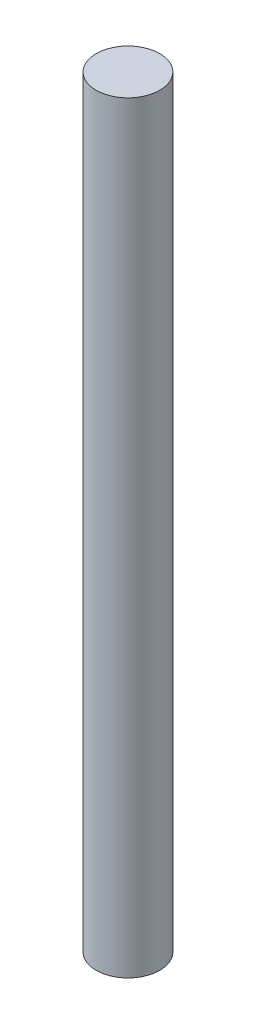
SolidWorks part; units mm, degrees
ref_plane "Front Plane" through (0, 0, 0) normal (0, 0, 1) x (1, 0, 0)
ref_plane "Top Plane" through (0, 0, 0) normal (0, 1, 0) x (1, 0, 0)
ref_plane "Right Plane" through (0, 0, 0) normal (1, 0, 0) x (0, 0, -1)
sketch "Sketch1" plane through (0, 0, 0) normal (0, 1, 0) x (1, 0, 0)
  circle A0 centre (0, 0) radius 30
  dimension "D1" = 60
extrude "Boss-Extrude1" add sketch "Sketch1" along normal blind 720
